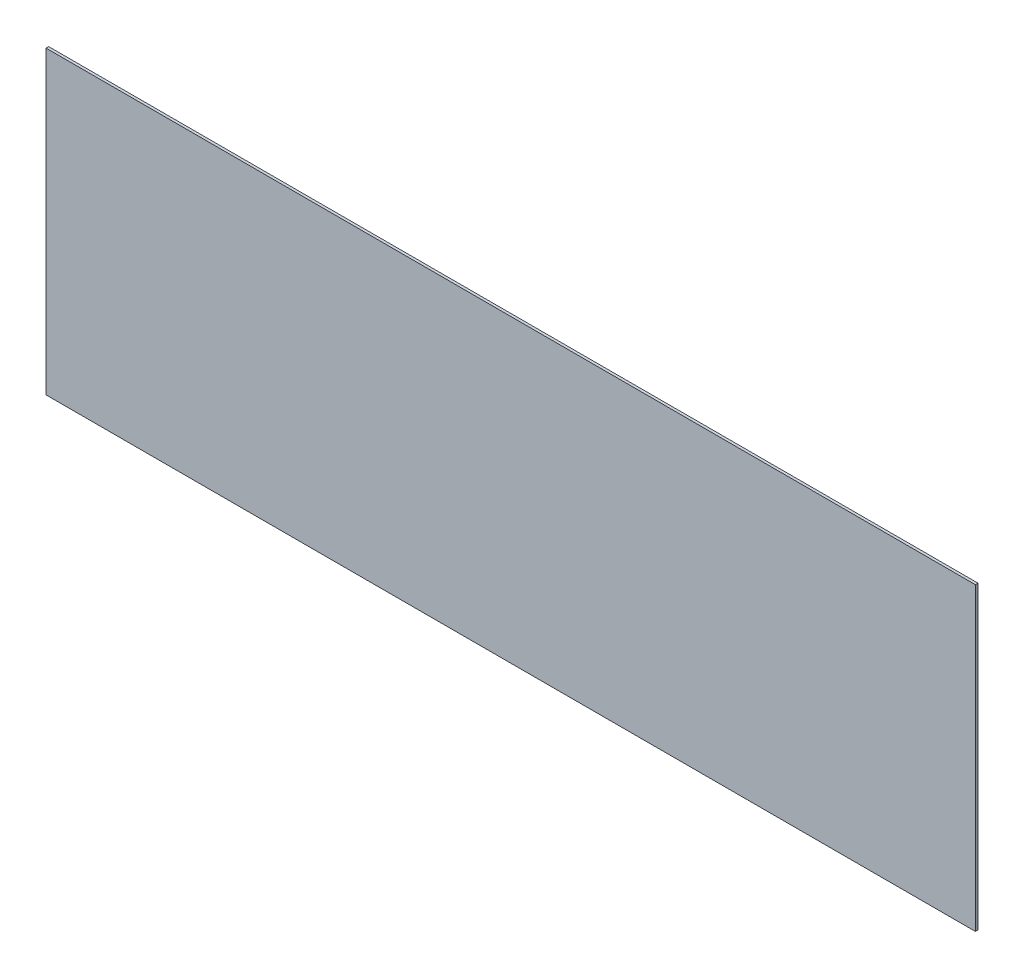
SolidWorks part; units mm, degrees
material "ABS PC"
ref_plane "Front Plane" through (0, 0, 0) normal (0, 0, 1) x (1, 0, 0)
ref_plane "Top Plane" through (0, 0, 0) normal (0, 1, 0) x (1, 0, 0)
ref_plane "Right Plane" through (0, 0, 0) normal (1, 0, 0) x (0, 0, -1)
sketch "Sketch1" plane through (0, 0, 0) normal (0, 0, 1) x (1, 0, 0)
  line L0 (61.722, -177.5302) -> (61.722, -72.3742) construction
  line L1 (61.722, -172.8154) -> (17.018, -172.8154)
  line L2 (61.722, -172.8154) -> (61.722, -158.3691)
  line L3 (61.722, -158.3691) -> (17.018, -158.3691)
  line L4 (17.018, -172.8154) -> (17.018, -158.3691)
  line L5 (61.722, -172.8154) -> (17.018, -158.3691) construction
  line L6 (61.722, -158.3691) -> (17.018, -172.8154) construction
  line L7 (17.018, -72.3742) -> (17.018, -177.5302) construction
  line L8 (39.37, -165.5922) -> (39.37, -158.3691) construction
  line L9 (39.37, -165.5922) -> (39.37, -172.8154) construction
  line L10 (60.452, -159.6391) -> (18.288, -159.6391) construction
  line L12 (18.288, -171.5454) -> (60.452, -171.5454) construction
  point P4 (39.37, -165.5922)
  dimension "D1" = 1.27
  dimension "D2" = 1.27
extrude "Boss-Extrude1" add sketch "Sketch1" along normal blind 0.127
